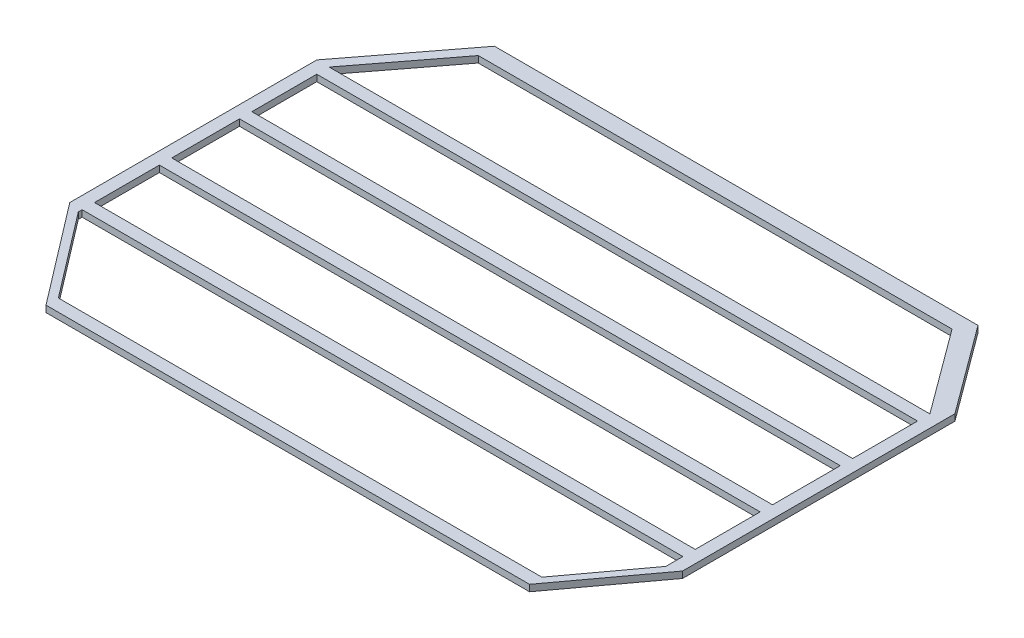
SolidWorks part; units mm, degrees
ref_plane "Front Plane" through (0, 0, 0) normal (0, 0, 1) x (1, 0, 0)
ref_plane "Top Plane" through (0, 0, 0) normal (0, 1, 0) x (1, 0, 0)
ref_plane "Right Plane" through (0, 0, 0) normal (1, 0, 0) x (0, 0, -1)
sketch "Sketch2" plane through (0, 0, 0) normal (0, 1, 0) x (1, 0, 0)
  line L0 (0, 0) -> (970, 0) construction
  line L3 (118.58, 345.4877) -> (863.58, 345.4877)
  line L6 (-117.2697, 0) -> (1303.2052, 0) construction
  line L7 (0, 190.295) -> (118.58, 345.4877)
  line L11 (963.71, 209.8289) -> (863.58, 345.4877)
  line L12 (0, 190.295) -> (0, -190.295)
  line L13 (963.71, 209.8289) -> (963.71, -209.8289)
  line L14 (963.71, -209.8289) -> (863.58, -345.4877)
  line L15 (0, -190.295) -> (118.58, -345.4877)
  line L16 (118.58, -345.4877) -> (863.58, -345.4877)
  point P8 (963.71, 0)
  point P10 (0, 0)
  point P12 (963.71, 0)
  point P18 (0, 0)
  dimension "D6" = 100.13
  dimension "D1" = 970
  dimension "D2" = 195.31
  dimension "D3" = 745
  dimension "D4" = 168.61
  dimension "D5" = 190.295
  dimension "D7" = 118.58
extrude "Boss-Extrude1" add sketch "Sketch2" along normal blind 10
sketch "Sketch3" plane through (0, 10, 0) normal (0, 1, 0) x (1, 0, 0)
  line L0 (0, 0) -> (1066.925, 0) construction
  line L1 (340, -245.4877) -> (340, -279.772)
  line L2 (340, -279.772) -> (341.6718, -281.96)
  line L3 (409.4844, -315.4877) -> (542.3855, -315.4877)
  line L4 (542.3855, -315.4877) -> (542.3855, -245.4877)
  line L5 (542.3855, -245.4877) -> (340, -245.4877)
  line L6 (0, -190.295) -> (118.58, -345.4877) construction
  line L10 (0, 190.295) -> (0, -190.295) construction
  line L11 (118.58, -345.4877) -> (863.58, -345.4877) construction
  arc A0 (341.6718, -281.96) -> (409.4844, -315.4877) centre (409.4844, -230.1456) ccw
  dimension "D3" = 85.3421
  dimension "D6" = 340
  dimension "D7" = 132.9011
  dimension "D5" = 85.3421
  dimension "D1" = 30
  dimension "D2" = 70
  dimension "D4" = 202.3855
sketch "Sketch5" plane through (0, 10, 0) normal (0, 1, 0) x (1, 0, 0)
  line L0 (708.71, 120) -> (708.71, 288.344)
  line L1 (708.71, 120) -> (908.71, 120)
  line L2 (908.71, 120) -> (908.71, 166.2721)
  line L3 (908.71, 166.2721) -> (825.5702, 278.9121)
  line L4 (806.8857, 288.344) -> (708.71, 288.344)
  line L8 (963.71, 209.8289) -> (863.58, 345.4877) construction
  line L9 (963.71, -209.8289) -> (963.71, 209.8289) construction
  line L10 (0, 0) -> (1246.4593, 0) construction
  arc A0 (825.5702, 278.9121) -> (806.8857, 288.344) centre (806.8857, 265.1211) ccw
  dimension "D1" = 140
  dimension "D2" = 46.2721
  dimension "D3" = 120
  dimension "D4" = 55
  dimension "D5" = 200
  dimension "D6" = 168.344
sketch "Sketch7" plane through (0, 10, 0) normal (0, 1, 0) x (1, 0, 0)
  line L5 (49.3094, 39.3239) -> (129.3094, 39.3239)
  line L6 (49.3094, 39.3239) -> (49.3094, -40.6761)
  line L7 (49.3094, -40.6761) -> (129.3094, -40.6761)
  line L8 (129.3094, 39.3239) -> (129.3094, -40.6761)
  dimension "D1" = 80
  dimension "D2" = 80
extrude "Cut-Extrude1" cut sketch "Sketch3" against normal blind 10
extrude "Boss-Extrude3" add sketch "Sketch7" along normal blind 10 and the other way blind 20
ref_plane "Plane1" through (481.855, 0, 0) normal (-1, 0, 0) x (0, 0, 1)
mirror "Mirror2" about plane through (481.855, 0, 0) normal (-1, 0, 0) of "Boss-Extrude3"
mirror "Mirror3" about plane through (0, 0, 0) normal (0, 0, 1) of "Cut-Extrude1"
sketch "Sketch8" plane through (0, 10, 0) normal (0, 1, 0) x (1, 0, 0)
  line L0 (0, 190.295) -> (963.71, 190.295) construction
  line L1 (963.71, -209.8289) -> (963.71, 209.8289) construction
  line L2 (963.71, 209.8289) -> (863.58, 345.4877) construction
  line L3 (19.05, 190.295) -> (19.05, -196.1769) construction
  line L4 (118.58, 345.4877) -> (118.58, -345.4877) construction
  line L5 (863.58, 345.4877) -> (863.58, -345.4877) construction
  line L6 (118.58, 345.4877) -> (0, 190.295) construction
  line L7 (0, -190.295) -> (118.58, -345.4877) construction
  line L8 (19.05, -196.1769) -> (118.58, -326.4377) construction
  line L9 (118.58, -326.4377) -> (863.58, -326.4377) construction
  line L10 (19.05, 190.295) -> (944.66, 190.295)
  line L11 (944.66, -190.2536) -> (944.66, 190.295) construction
  line L12 (863.58, -345.4877) -> (963.71, -209.8289) construction
  line L13 (19.05, 171.245) -> (944.66, 171.245)
  line L14 (19.05, 71.245) -> (944.66, 71.245)
  line L15 (0, 190.295) -> (0, -190.295) construction
  line L16 (19.05, 190.295) -> (19.05, -196.1769)
  line L17 (19.05, -196.1769) -> (118.58, -326.4377)
  line L18 (118.58, -326.4377) -> (863.58, -326.4377)
  line L19 (863.58, 345.4877) -> (118.58, 345.4877) construction
  line L20 (118.58, -345.4877) -> (863.58, -345.4877) construction
  line L29 (863.58, -326.4377) -> (944.66, -216.5884)
  line L30 (944.66, -216.5884) -> (944.66, 190.295)
  line L31 (944.66, 190.295) -> (848.5143, 320.5558)
  line L32 (848.5143, 320.5558) -> (118.58, 320.5558)
  line L33 (118.58, 320.5558) -> (19.05, 190.295)
  line L34 (19.05, 52.195) -> (944.66, 52.195)
  line L35 (0, 0) -> (1146.2236, 0) construction
  line L36 (19.05, -52.195) -> (944.66, -52.195)
  line L37 (19.05, -71.245) -> (944.66, -71.245)
  line L38 (19.05, -171.245) -> (944.66, -171.245)
  line L39 (19.05, -190.295) -> (944.66, -190.295)
  line M13 (49.3094, -40.6761) -> (49.3094, 39.3239)
  line M14 (49.3094, 39.3239) -> (129.3094, 39.3239)
  line M15 (129.3094, 39.3239) -> (129.3094, -40.6761)
  line M16 (129.3094, -40.6761) -> (49.3094, -40.6761)
  line M17 (340, -245.4877) -> (542.3855, -245.4877)
  line M18 (542.3855, -245.4877) -> (542.3855, -315.4877)
  line M19 (542.3855, -315.4877) -> (409.4844, -315.4877)
  arc M20 (409.4844, -315.4877) -> (341.6718, -281.96) centre (409.4844, -230.1456) cw
  line M21 (341.6718, -281.96) -> (340, -279.772)
  line M22 (340, -279.772) -> (340, -245.4877)
  line M31 (834.4006, 39.3239) -> (914.4006, 39.3239)
  line M32 (914.4006, 39.3239) -> (914.4006, -40.6761)
  line M33 (914.4006, -40.6761) -> (834.4006, -40.6761)
  line M34 (834.4006, -40.6761) -> (834.4006, 39.3239)
  line M35 (542.3855, 315.4877) -> (542.3855, 245.4877)
  line M36 (542.3855, 245.4877) -> (340, 245.4877)
  line M37 (340, 245.4877) -> (340, 279.772)
  line M38 (340, 279.772) -> (341.6718, 281.96)
  arc M39 (341.6718, 281.96) -> (409.4844, 315.4877) centre (409.4844, 230.1456) cw
  line M40 (409.4844, 315.4877) -> (542.3855, 315.4877)
  dimension "D1" = 19.05
  dimension "D2" = 19.05
  dimension "D3" = 19.05
  dimension "D4" = 19.05
  dimension "D5" = 19.05
  dimension "D6" = 100
extrude "Cut-Extrude6" cut sketch "Sketch8" against normal blind 10 contours L32 L33 L10 L31 M40 M35 M36 M37 M38 M39 | L14 L30 L13 L16 | L16 L36 L30 L34 M34 M31 M32 M33 M16 M13 M14 M15 | L16 L38 L30 L37 | L39 L16 L17 L18 L29 L30 M22 M17 M18 M19 M20 M21
